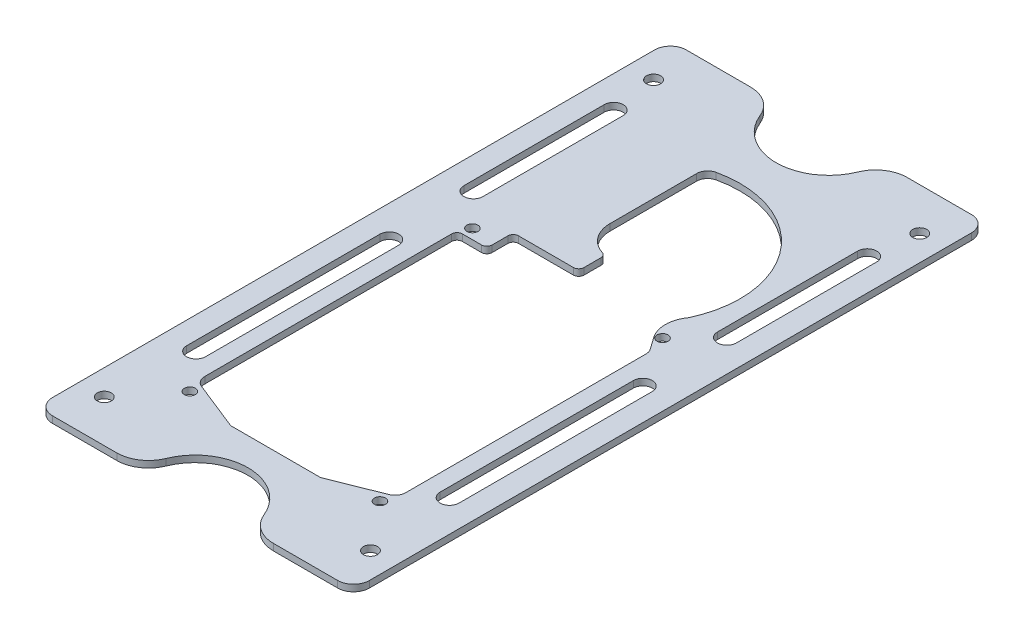
SolidWorks part; units mm, degrees
material "6061-T6 (SS)"
ref_plane "Front Plane" through (0, 0, 0) normal (0, 0, 1) x (1, 0, 0)
ref_plane "Top Plane" through (0, 0, 0) normal (0, 1, 0) x (1, 0, 0)
ref_plane "Right Plane" through (0, 0, 0) normal (1, 0, 0) x (0, 0, -1)
sketch "Sketch1" plane through (0, 0, 0) normal (0, 1, 0) x (1, 0, 0)
  line L1 (-76.2, 152.4) -> (76.2, 152.4)
  line L2 (-76.2, 152.4) -> (-76.2, -152.4)
  line L3 (-76.2, -152.4) -> (76.2, -152.4)
  line L4 (76.2, 152.4) -> (76.2, -152.4)
  line L5 (-76.2, 152.4) -> (76.2, -152.4) construction
  line L6 (-76.2, -152.4) -> (76.2, 152.4) construction
  point P0 (0, 0)
  dimension "D1" = 152.4
  dimension "D2" = 304.8
extrude "Boss-Extrude1" add sketch "Sketch1" along normal mid plane 3.175
sketch "Sketch3" plane through (0, 1.5875, 0) normal (0, 1, 0) x (1, 0, 0)
  line L0 (-50.8, -114.3) -> (50.8, -114.3) construction
  line L1 (-50.8, -114.3) -> (-50.8, 114.3) construction
  line L2 (-50.8, 114.3) -> (50.8, 114.3) construction
  line L3 (50.8, 114.3) -> (50.8, -114.3) construction
  line L4 (-50.8, 80.4579) -> (-76.2, 80.4579) construction
  line L5 (-76.2, 152.4) -> (-76.2, -152.4) construction
  line L6 (50.8, 80.4579) -> (76.2, 80.4579) construction
  line L7 (76.2, -152.4) -> (76.2, 152.4) construction
  line L8 (0, 114.3) -> (0, 152.4) construction
  line L9 (76.2, 152.4) -> (-76.2, 152.4) construction
  line L10 (0, -114.3) -> (0, -152.4) construction
  line L11 (-76.2, -152.4) -> (76.2, -152.4) construction
  line L12 (64.008, -132.08) -> (76.2, -132.08) construction
  line L13 (64.008, 132.08) -> (76.2, 132.08) construction
  line L14 (64.008, 132.08) -> (64.008, 152.4) construction
  line L15 (64.008, -132.08) -> (64.008, -152.4) construction
  circle A0 centre (45.72, -109.22) radius 2.6543
  circle A1 centre (45.72, 26.67) radius 2.6543
  circle A2 centre (64.008, 132.08) radius 3.3782
  circle A3 centre (64.008, -132.08) radius 3.3782
  dimension "D3" = 5.3086
  dimension "D7" = 6.7564
  dimension "D9" = 6.7564
  dimension "D1" = 101.6
  dimension "D2" = 228.6
  dimension "D4" = 5.08
  dimension "D5" = 135.89
  dimension "D6" = 5.08
  dimension "D8" = 12.192
  dimension "D11" = 20.32
extrude "Cut-Extrude1" cut sketch "Sketch3" against normal through all
mirror "Mirror1" about plane through (0, 0, 0) normal (1, 0, 0) of "Cut-Extrude1"
fillet "Fillet1" radius 7.62 4 edges at (76.2, 0, -152.4) (76.2, 0, 152.4) (-76.2, 0, 152.4) (-76.2, 0, -152.4)
sketch "Sketch4" plane through (0, 1.5875, 0) normal (0, 1, 0) x (1, 0, 0)
  line L0 (68.58, 152.4) -> (-68.58, 152.4) construction
  line L1 (37.6743, 152.4) -> (68.58, 152.4)
  line L2 (-37.6743, 152.4) -> (-68.58, 152.4)
  arc A0 (-23.5464, 142.875) -> (23.5464, 142.875) centre (0, 152.4) ccw
  arc A1 (-37.6743, 152.4) -> (-23.5464, 142.875) centre (-37.6743, 137.16) cw
  arc A2 (37.6743, 152.4) -> (23.5464, 142.875) centre (37.6743, 137.16) ccw
  point P11 (-25.4, 152.4)
  point P14 (25.4, 152.4)
  dimension "D1" = 50.8
  dimension "D2" = 15.24
  dimension "D3" = 15.24
extrude "Cut-Extrude2" cut sketch "Sketch4" against normal through all and the other way through all
mirror "Mirror2" about plane through (0, 0, 0) normal (0, 0, 1) of "Cut-Extrude2"
sketch "Sketch7" plane through (0, 1.5875, 0) normal (0, 1, 0) x (1, 0, 0)
  line L0 (60.96, 109.8775) -> (60.96, 42.4058) construction
  line L1 (65.5189, 109.8775) -> (65.5189, 42.4058)
  line L2 (56.4011, 109.8775) -> (56.4011, 42.4058)
  line L3 (60.96, 1.9736) -> (60.96, -90.9904) construction
  line L4 (65.5189, 1.9736) -> (65.5189, -90.9904)
  line L5 (56.4011, 1.9736) -> (56.4011, -90.9904)
  line L6 (68.58, 152.4) -> (37.6743, 152.4) construction
  line L7 (76.2, -144.78) -> (76.2, 144.78) construction
  arc A0 (65.5189, 109.8775) -> (56.4011, 109.8775) centre (60.96, 109.8775) ccw
  arc A1 (56.4011, 42.4058) -> (65.5189, 42.4058) centre (60.96, 42.4058) ccw
  arc A2 (65.5189, 1.9736) -> (56.4011, 1.9736) centre (60.96, 1.9736) ccw
  arc A3 (56.4011, -90.9904) -> (65.5189, -90.9904) centre (60.96, -90.9904) ccw
  point P2 (60.96, 76.1416)
  point P7 (60.96, -44.5084)
  dimension "D1" = 67.4717
  dimension "D2" = 92.964
  dimension "D3" = 120.65
  dimension "D4" = 76.2584
  dimension "D5" = 15.24
extrude "Cut-Extrude3" cut sketch "Sketch7" against normal through all
mirror "Mirror3" about plane through (0, 0, 0) normal (1, 0, 0) of "Cut-Extrude3"
sketch "Sketch9" plane through (0, -1.5875, 0) normal (0, -1, 0) x (1, 0, 0)
  line L0 (-14.5923, -61.722) -> (-14.5923, -103.3982)
  line L1 (48.3743, -16.0428) -> (48.3743, 99.3742)
  line L2 (21.6176, 113.6523) -> (45.0339, 104.3045)
  line L3 (-21.6176, 113.6523) -> (21.6176, 113.6523)
  line L4 (-45.0339, 104.3045) -> (-21.6176, 113.6523)
  line L5 (-48.3743, 99.3742) -> (-48.3743, -19.3887)
  line L6 (-45.8343, -21.9287) -> (-36.576, -21.9287)
  line L7 (-34.036, -24.4687) -> (-34.036, -32.0887)
  line L8 (-31.496, -34.6287) -> (-5.08, -34.6287)
  line L9 (-2.54, -37.1687) -> (-2.54, -45.3602)
  line L10 (43.3916, -24.7519) -> (47.3938, -19.1167)
  arc A0 (-14.5923, -103.3982) -> (-10.4379, -108.5798) centre (-9.2837, -103.3982) ccw
  arc A1 (-10.4379, -108.5798) -> (43.5297, -41.4792) centre (0, -61.722) ccw
  arc A2 (43.5297, -41.4792) -> (43.3916, -24.7519) centre (55.0333, -33.02) cw
  arc A3 (45.0339, 104.3045) -> (48.3743, 99.3742) centre (43.0657, 99.3742) cw
  arc A4 (-48.3743, 99.3742) -> (-45.0339, 104.3045) centre (-43.0657, 99.3742) cw
  arc A5 (-14.5923, -61.722) -> (-4.3268, -47.7859) centre (0, -61.722) cw
  arc A6 (-4.3268, -47.7859) -> (-2.54, -45.3602) centre (-5.08, -45.3602) ccw
  arc A7 (-5.08, -34.6287) -> (-2.54, -37.1687) centre (-5.08, -37.1687) cw
  arc A8 (-34.036, -32.0887) -> (-31.496, -34.6287) centre (-31.496, -32.0887) ccw
  arc A9 (-36.576, -21.9287) -> (-34.036, -24.4687) centre (-36.576, -24.4687) cw
  arc A10 (-48.3743, -19.3887) -> (-45.8343, -21.9287) centre (-45.8343, -19.3887) ccw
  arc A11 (47.3938, -19.1167) -> (48.3743, -16.0428) centre (43.0657, -16.0428) ccw
extrude "Cut-Extrude4" cut sketch "Sketch9" against normal through all
